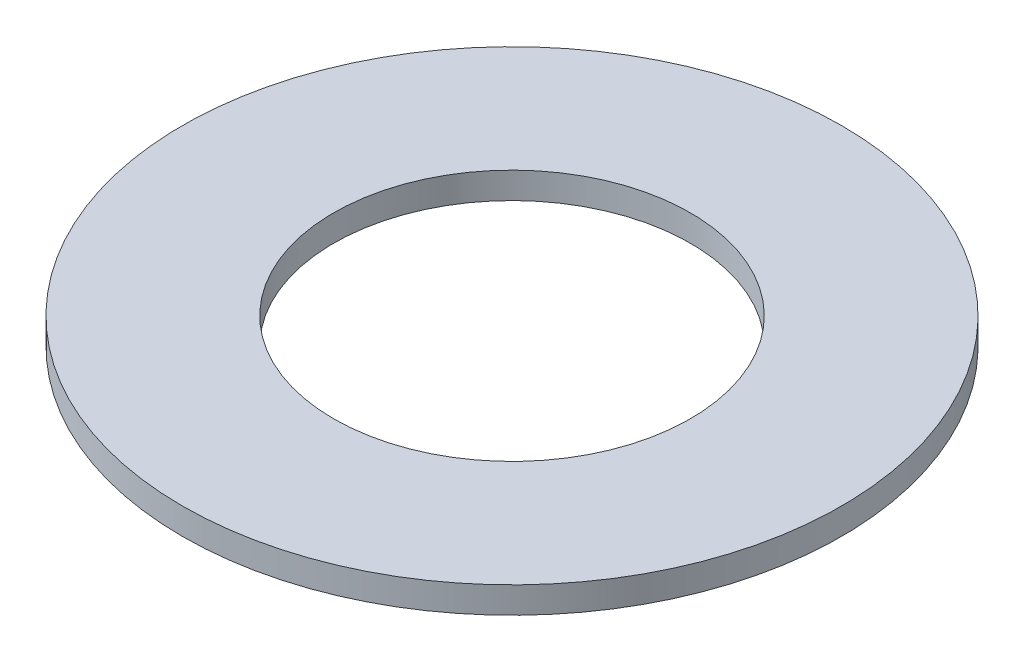
SolidWorks part; units mm, degrees
ref_plane "Front Plane" through (0, 0, 0) normal (0, 0, 1) x (1, 0, 0)
ref_plane "Top Plane" through (0, 0, 0) normal (0, 1, 0) x (1, 0, 0)
ref_plane "Right Plane" through (0, 0, 0) normal (1, 0, 0) x (0, 0, -1)
sketch "Sketch1" plane through (0, 0, 0) normal (0, 1, 0) x (1, 0, 0)
  circle A0 centre (0, 0) radius 19.05
  dimension "OD" = 38.1
extrude "Boss-Extrude1" add sketch "Sketch1" along normal blind 1.524
sketch "Sketch5" plane through (0, 1.524, 0) normal (0, 1, 0) x (-1, 0, 0)
  circle A0 centre (0, 0) radius 10.3124
  dimension "ID" = 20.6248
extrude "Cut-Extrude1" cut sketch "Sketch5" against normal through all
